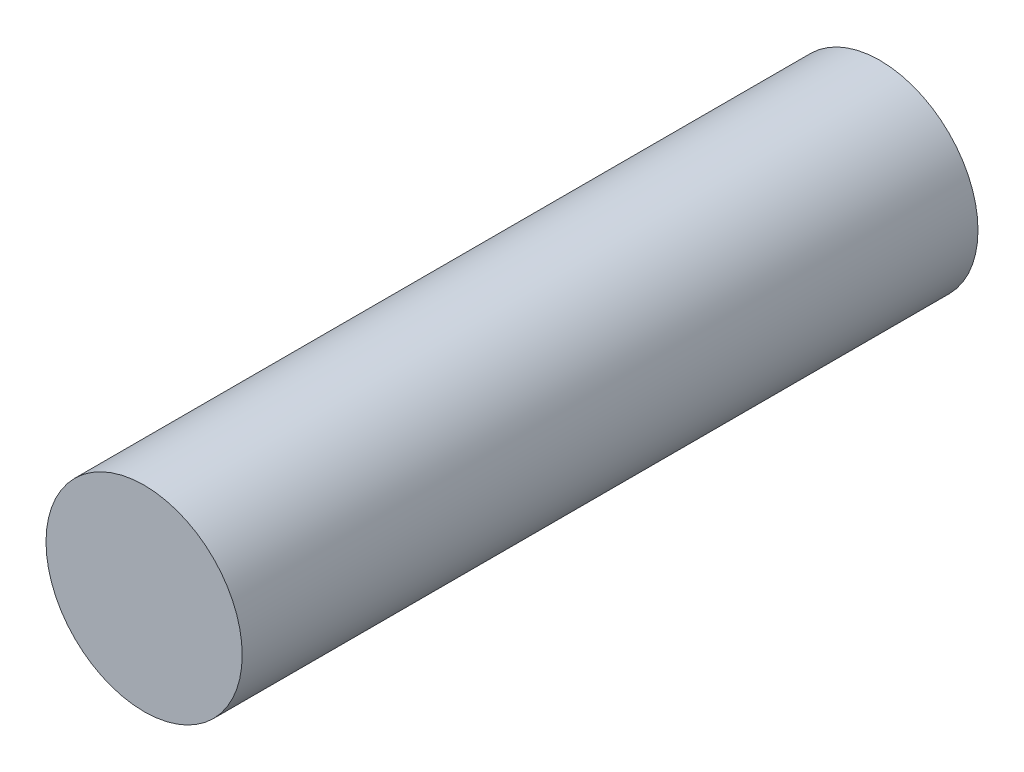
SolidWorks part; units mm, degrees
ref_plane "Front Plane" through (0, 0, 0) normal (0, 0, 1) x (1, 0, 0)
ref_plane "Top Plane" through (0, 0, 0) normal (0, 1, 0) x (1, 0, 0)
ref_plane "Right Plane" through (0, 0, 0) normal (1, 0, 0) x (0, 0, -1)
sketch "Sketch1" plane through (0, 0, 0) normal (0, 0, 1) x (1, 0, 0)
  circle A0 centre (0, 0) radius 4
  dimension "D1" = 8
extrude "Boss-Extrude1" add sketch "Sketch1" along normal blind 60
sketch "Sketch2" [suppressed] plane through (0, 0, 60) normal (0, 0, 1) x (1, 0, 0)
  circle A1 centre (0, 0) radius 4
  circle A2 centre (0, 0) radius 4
  dimension "D1" = 0
extrude "Boss-Extrude2" [suppressed] add sketch "Sketch2" along normal blind 25
sketch "Sketch3" plane through (0, 0, 60) normal (0, 0, 1) x (1, 0, 0)
  circle A1 centre (0, 0) radius 4
  circle A2 centre (0, 0) radius 4
  dimension "D1" = 0
extrude "Cut-Extrude1" cut sketch "Sketch3" against normal blind 30
